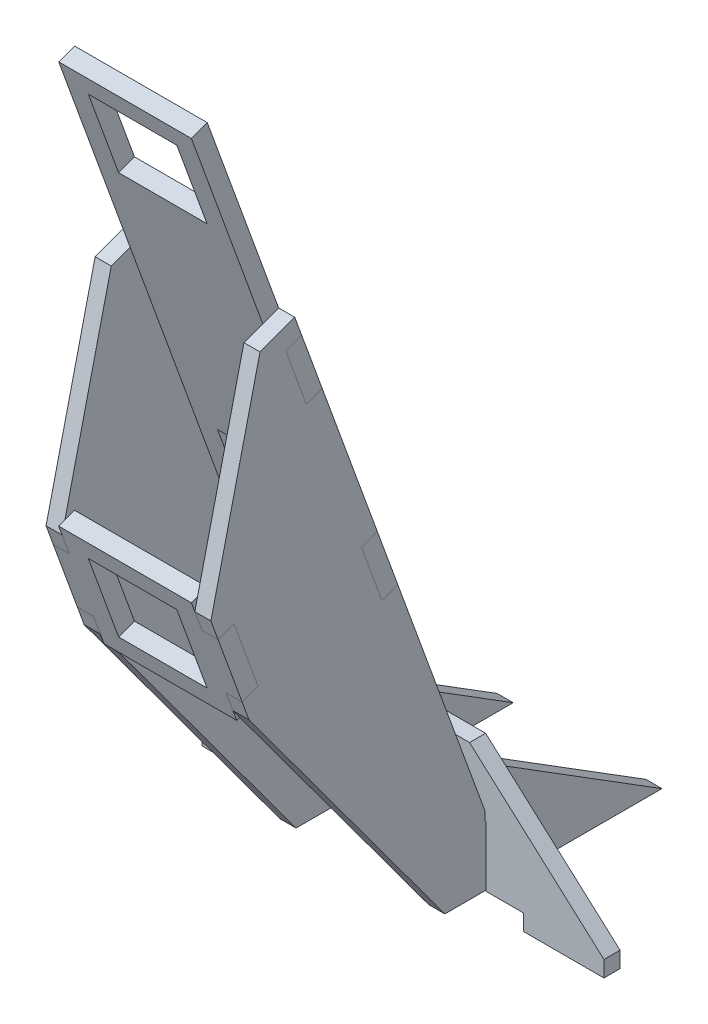
SolidWorks part; units mm, degrees
ref_plane "Front Plane" through (0, 0, 0) normal (0, 0, 1) x (1, 0, 0)
ref_plane "Top Plane" through (0, 0, 0) normal (0, 1, 0) x (1, 0, 0)
ref_plane "Right Plane" through (0, 0, 0) normal (1, 0, 0) x (0, 0, -1)
sketch "Sketch2" plane through (-4.2325, 0, 0) normal (-1, 0, 0) x (0, 0, 1)
  line L0 (-218.5461, -194.3785) -> (8.2017, -276.908) construction
  line L1 (-1207.3778, 14.2537) -> (0.4005, -425.3416) construction
  line L2 (-218.5461, -321.3785) -> (8.2017, -403.908) construction
  line L3 (-1207.3778, 141.2537) -> (0.4005, -298.3416) construction
  line L4 (-208.1635, -198.1575) -> (8.2017, -276.908)
  line L5 (-207.799, -349.5632) -> (0.4005, -425.3416)
  line L6 (-208.0044, -325.2154) -> (8.2017, -403.908)
  line L7 (-208.2509, -222.3987) -> (0.4005, -298.3416)
  spline S0 degree 3 poles (189.4409, -3120.4084) (-13.0982, -2399.0287) (-141.5864, -1647.8741) (-189.7389, -873.9266) (-192.938, -817.645) (-195.5222, -767.4363) (-197.2853, -729.899) (-199.779, -673.587) (-201.7119, -622.7867) (-203.4957, -566.448) (-206.2171, -472.5416) (-207.9041, -370.9386) (-208.259, -276.9662) (-208.2899, -248.7729) (-208.2187, -160.2224) (-207.0238, -66.2188) (-203.9584, 56.001) (-202.3756, 119.8355) (-200.5061, 195.0475) (-179.7563, 1029.0685) (-159.4327, 1846.2624) (-139.564, 2642.678) knots -1.099268 -1.099268 -1.099268 -1.099268 0.127744 0.158994 0.190244 0.221494 0.242608 0.252744 0.315244 0.327161 0.346494 0.471494 0.496149 0.502744 0.518369 0.643369 0.658994 0.721494 0.74946 0.783994 2.107611 2.107611 2.107611 2.107611 only from (-169.1687, -1155.1044) to (-189.3532, 643.3419) construction
  spline S1 degree 3 poles (-169.1687, -1155.1044) (-175.6459, -1080.1785) (-182.7373, -986.4616) (-189.7389, -873.9266) (-192.938, -817.645) (-195.5222, -767.4363) (-197.2853, -729.899) (-199.779, -673.587) (-201.7119, -622.7867) (-203.4957, -566.448) (-206.2171, -472.5416) (-207.9041, -370.9386) (-208.259, -276.9662) (-208.2899, -248.7729) (-208.2187, -160.2224) (-207.0238, -66.2188) (-203.9584, 56.001) (-202.3756, 119.8355) (-200.5061, 195.0475) (-196.3369, 362.6233) (-192.5867, 513.3721) (-189.3532, 643.3419) knots 0.002744 0.002744 0.002744 0.002744 0.127744 0.158994 0.190244 0.221494 0.242608 0.252744 0.315244 0.327161 0.346494 0.471494 0.496149 0.502744 0.518369 0.643369 0.658994 0.721494 0.74946 0.783994 1 1 1 1
sketch "Sketch3" plane through (0, 0, 0) normal (1, 0, 0) x (0, 0, -1)
  line L0 (-6.4471, -266.1331) -> (-11.4594, -267.9574)
  line L1 (-6.4471, -266.1331) -> (48.6866, -417.6117)
  line L2 (-11.4594, -267.9574) -> (43.6743, -419.436)
  line L3 (48.6866, -417.6117) -> (43.6743, -419.436)
  line L5 (208.1635, -198.1575) -> (-8.2017, -276.908) construction
  line L6 (207.799, -349.5632) -> (-0.4005, -425.3416) construction
  line L7 (7.8696, -432.4678) -> (2.8573, -434.2922)
  line L8 (7.8696, -432.4678) -> (-6.4471, -393.1331)
  line L9 (2.8573, -434.2922) -> (-11.4594, -394.9574)
  line L10 (-6.4471, -393.1331) -> (-11.4594, -394.9574)
  line L11 (208.0044, -325.2154) -> (-8.2017, -403.908) construction
  point P9 (46.1804, -418.5238)
  dimension "D1" = 5.334
  dimension "D2" = 9.525
  dimension "D3" = 9.525
  dimension "D4" = 9.525
extrude "Boss-Extrude1" add sketch "Sketch3" against normal blind 13.335 and the other way blind 28.575 contours L2 L3 L1 L0
sketch "Sketch4" plane through (0, -33.2037, 91.2265) normal (0, 0.342, -0.9397) x (-1, 0, 0)
  line L0 (3.7846, -399.5534) -> (-19.0246, -399.5534) construction
  line L1 (3.7846, -399.5534) -> (3.7846, -376.7442) construction
  line L2 (-19.0246, -399.5534) -> (-19.0246, -376.7442) construction
  line L3 (3.7846, -376.7442) -> (-19.0246, -376.7442) construction
  line L4 (3.7846, -280.2124) -> (3.7846, -257.4032) construction
  line L5 (3.7846, -280.2124) -> (-19.0246, -280.2124) construction
  line L6 (3.7846, -257.4032) -> (-19.0246, -257.4032) construction
  line L7 (-19.0246, -280.2124) -> (-19.0246, -257.4032) construction
  line L9 (-28.575, -409.0784) -> (13.335, -409.0784) construction
  line L10 (-21.59, -282.7778) -> (-21.59, -254.8378)
  line L11 (6.35, -254.8378) -> (-21.59, -254.8378)
  line L12 (6.35, -282.7778) -> (6.35, -254.8378)
  line L13 (6.35, -282.7778) -> (-21.59, -282.7778)
  line L14 (6.35, -374.1788) -> (-21.59, -374.1788)
  line L15 (-21.59, -402.1188) -> (-21.59, -374.1788)
  line L16 (6.35, -402.1188) -> (-21.59, -402.1188)
  line L17 (6.35, -402.1188) -> (6.35, -374.1788)
  point P0 (4.2325, -399.5534)
  point P3 (4.2325, -376.7442)
  point P6 (4.2325, -280.2124)
  point P9 (4.2325, -257.4032)
  point P19 (-7.62, -399.5534)
  point P22 (-7.62, -409.0784)
  dimension "D1" = 27.94
  dimension "D2" = 27.94
extrude "Cut-Extrude1" cut sketch "Sketch4" against normal through all
sketch "Sketch5" plane through (0, -515.0244, 0) normal (0, 1, 0) x (1, 0, 0)
  line L0 (223.6182, 76.2) -> (198.2182, 76.2) construction
  line L1 (198.2182, 81.28) -> (223.6182, 81.28) construction
  line L2 (172.8182, 76.2) -> (147.4182, 76.2) construction
  line L3 (147.4182, 81.28) -> (172.8182, 81.28) construction
  line L4 (20.4182, 198.4309) -> (-4.9818, 198.4309)
  line L5 (-4.9818, 198.4309) -> (-4.9818, 204.5203)
  line L6 (-219.8374, 5.08) -> (235.2738, 5.08)
  line L7 (20.4182, 204.5202) -> (20.4182, 198.4309)
  line L8 (20.4182, 198.4309) -> (-4.9818, 198.4309)
  line L9 (-4.9818, 198.4309) -> (-4.9818, 204.5203)
  line L10 (-219.8374, 5.08) -> (235.2738, 5.08)
  line L11 (20.4182, 204.5202) -> (20.4182, 198.4309)
  line L12 (122.0182, 76.2) -> (96.6182, 76.2) construction
  line L13 (96.6182, 81.28) -> (122.0182, 81.28) construction
  line L14 (45.8182, 81.28) -> (71.2182, 81.28) construction
  line L15 (71.2182, 76.2) -> (45.8182, 76.2) construction
  line L16 (20.4182, 76.2) -> (-4.9818, 76.2) construction
  line L17 (-4.9818, 81.28) -> (20.4182, 81.28) construction
  line L18 (-30.3818, 76.2) -> (-55.7818, 76.2) construction
  line L19 (-55.7818, 81.28) -> (-30.3818, 81.28) construction
  line L20 (-81.1818, 76.2) -> (-106.5818, 76.2) construction
  line L21 (-106.5818, 81.28) -> (-81.1818, 81.28) construction
  line L22 (-131.9818, 76.2) -> (-157.3818, 76.2) construction
  line L23 (-157.3818, 81.28) -> (-131.9818, 81.28) construction
  line L24 (-182.7818, 76.2) -> (-208.1818, 76.2) construction
  line L25 (-208.1818, 81.28) -> (-182.7818, 81.28) construction
  line L26 (-208.1818, 81.28) -> (-182.7818, 81.28)
  line L27 (-182.7818, 76.2) -> (-208.1818, 76.2)
  line L28 (-157.3818, 81.28) -> (-131.9818, 81.28)
  line L29 (-131.9818, 76.2) -> (-157.3818, 76.2)
  line L30 (-106.5818, 81.28) -> (-81.1818, 81.28)
  line L31 (-81.1818, 76.2) -> (-106.5818, 76.2)
  line L32 (-55.7818, 81.28) -> (-30.3818, 81.28)
  line L33 (-30.3818, 76.2) -> (-55.7818, 76.2)
  line L34 (-4.9818, 81.28) -> (20.4182, 81.28)
  line L35 (20.4182, 76.2) -> (-4.9818, 76.2)
  line L36 (45.8182, 81.28) -> (71.2182, 81.28)
  line L37 (71.2182, 76.2) -> (45.8182, 76.2)
  line L38 (96.6182, 81.28) -> (122.0182, 81.28)
  line L39 (122.0182, 76.2) -> (96.6182, 76.2)
  line L40 (147.4182, 81.28) -> (172.8182, 81.28)
  line L41 (172.8182, 76.2) -> (147.4182, 76.2)
  line L42 (198.2182, 81.28) -> (223.6182, 81.28)
  line L43 (223.6182, 76.2) -> (198.2182, 76.2)
  spline S2 degree 3 poles (1842.4663, -3260.0665) (948.577, -533.6156) (383.6873, 261.2248) (-42.8345, 200.7019) (-49.9403, 199.4383) (-64.0669, 196.4116) (-71.0878, 194.6489) (-81.5541, 191.6239) (-85.0321, 190.552) (-90.2326, 188.8477) (-91.9634, 188.2636) (-95.4194, 187.0627) (-97.1424, 186.4468) (-105.7114, 183.2977) (-112.4394, 180.5492) (-132.2531, 171.6351) (-144.9698, 164.804) (-163.3071, 153.2264) (-169.2964, 149.1452) (-178.0924, 142.6841) (-180.993, 140.4738) (-185.2959, 137.0716) (-186.7221, 135.9231) (-188.4878, 134.475) (-188.8401, 134.1847) (-189.5433, 133.6027) (-189.8953, 133.312) (-190.9356, 132.426) (-191.6104, 131.8185) (-194.8949, 128.7004) (-197.2373, 125.9495) (-199.8047, 122.1867) (-200.3, 121.4179) (-201.2541, 119.8473) (-201.7134, 119.0436) (-203.0281, 116.5915) (-203.806, 114.93) (-205.1764, 111.5567) (-205.768, 109.8447) (-206.7675, 106.3707) (-207.1764, 104.6091) (-207.5683, 102.3747) (-207.6407, 101.9262) (-207.7733, 101.0259) (-207.8317, 100.5736) (-208.0056, 99.2163) (-208.1214, 98.3115) (-208.4688, 95.5968) (-208.7001, 93.787) (-356.7457, -1065.9382) (-390.3223, -2238.1969) (-2268.9649, -3178.7947) knots -3.541724 -3.541724 -3.541724 -3.541724 0.125 0.125 0.1875 0.1875 0.25 0.25 0.28125 0.28125 0.296875 0.296875 0.3125 0.3125 0.375 0.375 0.5 0.5 0.5625 0.5625 0.59375 0.59375 0.609375 0.609375 0.613281 0.613281 0.617188 0.617188 0.625 0.625 0.65625 0.65625 0.664063 0.664063 0.671875 0.671875 0.6875 0.6875 0.703125 0.703125 0.71875 0.71875 0.722656 0.722656 0.726563 0.726563 0.734375 0.734375 0.75 0.75 10.746502 10.746502 10.746502 10.746502 only from (-4.9818, 204.5203) to (-219.8374, 5.08)
  spline S3 degree 3 poles (2354.6207, -3093.6099) (407.0316, -2276.1632) (374.4311, -1083.5388) (224.132, 93.8227) (223.7849, 96.5384) (223.4372, 99.2541) (223.2632, 100.6119) (223.2044, 101.0644) (223.0708, 101.9667) (222.9978, 102.4169) (222.6018, 104.6625) (222.1869, 106.4428) (221.4197, 109.0896) (221.1394, 109.9678) (220.5289, 111.7161) (220.1999, 112.5817) (218.4502, 116.8405) (216.7095, 120.0562) (214.1102, 123.8382) (213.5687, 124.5824) (212.4417, 126.0462) (211.8552, 126.7671) (210.0517, 128.8641) (208.7846, 130.1839) (206.7909, 132.0516) (206.1106, 132.6552) (205.0667, 133.5322) (204.7161, 133.8213) (204.0152, 134.4001) (202.2598, 135.8431) (200.4883, 137.2667) (196.2056, 140.646) (193.3094, 142.8493) (187.4346, 147.1565) (184.4517, 149.2632) (178.4338, 153.3562) (175.3969, 155.344) (166.2039, 161.1335) (159.965, 164.7612) (147.2712, 171.561) (140.8164, 174.7336) (121.1292, 183.5717) (107.5758, 188.5606) (91.8269, 193.1168) (90.0694, 193.6084) (86.553, 194.5586) (84.7927, 195.0175) (79.5049, 196.3465) (75.9708, 197.1686) (65.3426, 199.4454) (58.2221, 200.7102) (-388.5399, 264.0224) (-958.4281, -616.7535) (-1775.0229, -3283.3786) knots -9.89492 -9.89492 -9.89492 -9.89492 0.25 0.25 0.265625 0.273438 0.273438 0.277344 0.277344 0.28125 0.28125 0.296875 0.296875 0.304688 0.304688 0.3125 0.3125 0.34375 0.34375 0.351563 0.351563 0.359375 0.359375 0.375 0.375 0.382813 0.382813 0.386719 0.386719 0.390625 0.40625 0.40625 0.4375 0.4375 0.46875 0.46875 0.5 0.5 0.5625 0.5625 0.625 0.625 0.75 0.75 0.765625 0.765625 0.78125 0.78125 0.8125 0.8125 0.875 0.875 4.714976 4.714976 4.714976 4.714976 only from (235.2738, 5.08) to (20.4182, 204.5202)
  spline S4 degree 3 poles (-4.9818, 204.5203) (-15.3035, 204.0961) (-25.5375, 203.1563) (-42.8345, 200.7019) (-49.9403, 199.4383) (-64.0669, 196.4116) (-71.0878, 194.6489) (-81.5541, 191.6239) (-85.0321, 190.552) (-90.2326, 188.8477) (-91.9634, 188.2636) (-95.4194, 187.0627) (-97.1424, 186.4468) (-105.7114, 183.2977) (-112.4394, 180.5492) (-132.2531, 171.6351) (-144.9698, 164.804) (-163.3071, 153.2264) (-169.2964, 149.1452) (-178.0924, 142.6841) (-180.993, 140.4738) (-185.2959, 137.0716) (-186.7221, 135.9231) (-188.4878, 134.475) (-188.8401, 134.1847) (-189.5433, 133.6027) (-189.8953, 133.312) (-190.9356, 132.426) (-191.6104, 131.8185) (-194.8949, 128.7004) (-197.2373, 125.9495) (-199.8047, 122.1867) (-200.3, 121.4179) (-201.2541, 119.8473) (-201.7134, 119.0436) (-203.0281, 116.5915) (-203.806, 114.93) (-205.1764, 111.5567) (-205.768, 109.8447) (-206.7675, 106.3707) (-207.1764, 104.6091) (-207.5683, 102.3747) (-207.6407, 101.9262) (-207.7733, 101.0259) (-207.8317, 100.5736) (-208.0056, 99.2163) (-208.1214, 98.3115) (-208.4688, 95.5968) (-208.7001, 93.787) (-212.6278, 63.0191) (-216.253, 34.0521) (-219.8374, 5.08) knots 0.036266 0.036266 0.036266 0.036266 0.125 0.125 0.1875 0.1875 0.25 0.25 0.28125 0.28125 0.296875 0.296875 0.3125 0.3125 0.375 0.375 0.5 0.5 0.5625 0.5625 0.59375 0.59375 0.609375 0.609375 0.613281 0.613281 0.617188 0.617188 0.625 0.625 0.65625 0.65625 0.664063 0.664063 0.671875 0.671875 0.6875 0.6875 0.703125 0.703125 0.71875 0.71875 0.722656 0.722656 0.726563 0.726563 0.734375 0.734375 0.75 0.75 1 1 1 1
  spline S5 degree 3 poles (235.2738, 5.08) (231.688, 34.0638) (228.0612, 63.0431) (224.132, 93.8227) (223.7849, 96.5384) (223.4372, 99.2541) (223.2632, 100.6119) (223.2044, 101.0644) (223.0708, 101.9667) (222.9978, 102.4169) (222.6018, 104.6625) (222.1869, 106.4428) (221.4197, 109.0896) (221.1394, 109.9678) (220.5289, 111.7161) (220.1999, 112.5817) (218.4502, 116.8405) (216.7095, 120.0562) (214.1102, 123.8382) (213.5687, 124.5824) (212.4417, 126.0462) (211.8552, 126.7671) (210.0517, 128.8641) (208.7846, 130.1839) (206.7909, 132.0516) (206.1106, 132.6552) (205.0667, 133.5322) (204.7161, 133.8213) (204.0152, 134.4001) (202.2598, 135.8431) (200.4883, 137.2667) (196.2056, 140.646) (193.3094, 142.8493) (187.4346, 147.1565) (184.4517, 149.2632) (178.4338, 153.3562) (175.3969, 155.344) (166.2039, 161.1335) (159.965, 164.7612) (147.2712, 171.561) (140.8164, 174.7336) (121.1292, 183.5717) (107.5758, 188.5606) (91.8269, 193.1168) (90.0694, 193.6084) (86.553, 194.5586) (84.7927, 195.0175) (79.5049, 196.3465) (75.9708, 197.1686) (65.3426, 199.4454) (58.2221, 200.7102) (40.9206, 203.162) (30.7048, 204.0975) (20.4182, 204.5202) knots 0 0 0 0 0.25 0.25 0.265625 0.273438 0.273438 0.277344 0.277344 0.28125 0.28125 0.296875 0.296875 0.304688 0.304688 0.3125 0.3125 0.34375 0.34375 0.351563 0.351563 0.359375 0.359375 0.375 0.375 0.382813 0.382813 0.386719 0.386719 0.390625 0.40625 0.40625 0.4375 0.4375 0.46875 0.46875 0.5 0.5 0.5625 0.5625 0.625 0.625 0.75 0.75 0.765625 0.765625 0.78125 0.78125 0.8125 0.8125 0.875 0.875 0.963629 0.963629 0.963629 0.963629
  dimension "D1" = 0
ref_plane "Plane1" through (0, 0, -76.2) normal (0, 0, 1) x (1, 0, 0)
sketch "Sketch6" plane through (0, 0, -76.2) normal (0, 0, 1) x (1, 0, 0)
  line L0 (71.2182, -515.0244) -> (45.8182, -515.0244)
  line L1 (71.2182, -515.0244) -> (71.2182, -520.1044)
  line L2 (45.8182, -515.0244) -> (45.8182, -520.1044)
  line L3 (71.2182, -520.1044) -> (45.8182, -520.1044)
  line L4 (20.4182, -515.0244) -> (-4.9818, -515.0244)
  line L5 (20.4182, -515.0244) -> (20.4182, -520.1044)
  line L6 (-4.9818, -515.0244) -> (-4.9818, -520.1044)
  line L7 (20.4182, -520.1044) -> (-4.9818, -520.1044)
  line L8 (-30.3818, -515.0244) -> (-55.7818, -515.0244)
  line L9 (-30.3818, -515.0244) -> (-30.3818, -520.1044)
  line L10 (-55.7818, -515.0244) -> (-55.7818, -520.1044)
  line L11 (-30.3818, -520.1044) -> (-55.7818, -520.1044)
  line L12 (45.8182, -515.0244) -> (20.4182, -515.0244)
  line L13 (-4.9818, -515.0244) -> (-30.3818, -515.0244)
  line L14 (-55.7818, -515.0244) -> (-13.335, -476.9244)
  line L15 (-13.335, -476.9244) -> (28.7714, -476.9244)
  line L16 (28.7714, -476.9244) -> (71.2182, -515.0244)
  line L17 (-13.335, -267.9574) -> (-13.335, -419.436) construction
  dimension "D1" = 5.08
  dimension "D2" = 38.1
extrude "Boss-Extrude2" add sketch "Sketch6" against normal blind 5.08 separate body contours L16 L15 L14 L8 L13 L4 L12 L0 | L3 L1 L0 L2 | L7 L5 L4 L6 | L11 L9 L8 L10
sketch "Sketch7" plane through (0, 0, -76.2) normal (0, 0, 1) x (1, 0, 0)
  line L0 (28.575, -515.0244) -> (33.909, -515.0244)
  line L1 (28.575, -515.0244) -> (28.575, -495.9744)
  line L2 (33.909, -515.0244) -> (33.909, -495.9744)
  line L3 (28.575, -495.9744) -> (33.909, -495.9744)
  line L4 (45.8182, -515.0244) -> (20.4182, -515.0244) construction
  line L5 (-13.335, -515.0244) -> (-18.669, -515.0244)
  line L6 (-13.335, -515.0244) -> (-13.335, -495.9744)
  line L7 (-18.669, -515.0244) -> (-18.669, -495.9744)
  line L8 (-13.335, -495.9744) -> (-18.669, -495.9744)
  line L9 (-4.9818, -515.0244) -> (-30.3818, -515.0244) construction
  line L10 (28.575, -267.9574) -> (28.575, -419.436) construction
  line L11 (-13.335, -267.9574) -> (-13.335, -419.436) construction
  dimension "D1" = 5.334
  dimension "D2" = 19.05
extrude "Cut-Extrude2" cut sketch "Sketch7" against normal through all
sketch "Sketch8" plane through (0, -49.8842, 137.0558) normal (0, -0.342, 0.9397) x (1, 0, 0)
  line L0 (-13.335, -377.0363) -> (-13.335, -399.2613)
  line L1 (-13.335, -377.0363) -> (-18.415, -377.0363)
  line L2 (-13.335, -399.2613) -> (-18.415, -399.2613)
  line L3 (-18.415, -377.0363) -> (-18.415, -399.2613)
  line L4 (-13.335, -367.2192) -> (-13.335, -409.0784) construction
  line L5 (28.575, -377.0363) -> (28.575, -399.2613)
  line L6 (28.575, -377.0363) -> (33.655, -377.0363)
  line L7 (28.575, -399.2613) -> (33.655, -399.2613)
  line L8 (33.655, -377.0363) -> (33.655, -399.2613)
  line L9 (28.575, -367.2192) -> (28.575, -409.0784) construction
  point P12 (28.575, -388.1488)
  point P13 (-13.335, -388.1488)
  dimension "D1" = 5.08
  dimension "D2" = 22.225
extrude "Boss-Extrude3" add sketch "Sketch8" against normal up to surface (5.334 mm away) up to face at (7.62, -412.8005, -0.7112)
sketch "Sketch10" plane through (0, -35.0281, 96.2388) normal (0, -0.342, 0.9397) x (1, 0, 0)
  line L0 (-13.335, -409.0784) -> (-13.335, -390.0284)
  line L1 (-13.335, -409.0784) -> (-18.415, -409.0784)
  line L2 (-13.335, -390.0284) -> (-18.415, -390.0284)
  line L3 (-18.415, -409.0784) -> (-18.415, -390.0284)
  line L4 (-13.335, -247.8782) -> (-13.335, -409.0784) construction
  line L5 (28.575, -409.0784) -> (28.575, -390.0284)
  line L6 (28.575, -409.0784) -> (33.655, -409.0784)
  line L7 (28.575, -390.0284) -> (33.655, -390.0284)
  line L8 (33.655, -409.0784) -> (33.655, -390.0284)
  line L9 (28.575, -247.8782) -> (28.575, -409.0784) construction
  line L10 (-13.335, -320.1784) -> (-13.335, -339.2284)
  line L11 (-13.335, -320.1784) -> (-18.415, -320.1784)
  line L12 (-13.335, -339.2284) -> (-18.415, -339.2284)
  line L13 (-18.415, -320.1784) -> (-18.415, -339.2284)
  line L14 (28.575, -320.1784) -> (28.575, -339.2284)
  line L15 (28.575, -320.1784) -> (33.655, -320.1784)
  line L16 (28.575, -339.2284) -> (33.655, -339.2284)
  line L17 (33.655, -320.1784) -> (33.655, -339.2284)
  dimension "D1" = 5.08
  dimension "D2" = 19.05
  dimension "D3" = 88.9
extrude "Boss-Extrude4" add sketch "Sketch10" against normal up to surface (5.334 mm away) up to face at (7.62, -285.8005, -0.7112)
sketch "Sketch11" plane through (-13.335, 0, 0) normal (-1, 0, 0) x (0, 0, 1)
  line L0 (-16.1092, -328.1059) -> (-5.1298, -332.1021)
  line L1 (10.3735, -397.9409) -> (-1.6714, -431.0342)
  line L3 (-16.1092, -328.1059) -> (-76.2, -493.2041)
  line L4 (-42.1711, -399.7105) -> (-24.7965, -351.9741) construction
  line L5 (-76.2, -493.2041) -> (-76.2, -495.9744)
  line L8 (-63.5, -515.0244) -> (-132.08, -515.0244)
  line L9 (-132.08, -515.0244) -> (-81.28, -483.2744)
  line L10 (10.3735, -397.9409) -> (-5.1298, -332.1021)
  line L12 (-208.0044, -325.2154) -> (8.2017, -403.908) construction
  line L13 (-81.28, -483.2744) -> (-81.28, -495.9744)
  line L14 (-81.28, -495.9744) -> (-76.2, -495.9744)
  line L15 (-81.28, -495.9744) -> (-76.2, -495.9744) construction
  line L16 (-18.281, -334.073) -> (-13.2687, -335.8973) construction
  line L17 (-13.2687, -335.8973) -> (-19.7842, -353.7985) construction
  line L18 (-18.281, -334.073) -> (-24.7965, -351.9741) construction
  line L19 (-24.7965, -351.9741) -> (-19.7842, -353.7985) construction
  line L20 (-19.7842, -353.7985) -> (-13.2687, -335.8973) construction
  line L21 (-13.2687, -335.8973) -> (-18.281, -334.073) construction
  line L22 (3.0895, -402.3581) -> (-4.5119, -423.2428) construction
  line L23 (-4.5119, -423.2428) -> (0.5004, -425.0671) construction
  line L24 (0.5004, -425.0671) -> (8.1018, -404.1825) construction
  line L25 (8.1018, -404.1825) -> (3.0895, -402.3581) construction
  line L26 (-42.1711, -399.7105) -> (-48.6866, -417.6117) construction
  line L27 (-48.6866, -417.6117) -> (-43.6743, -419.436) construction
  line L28 (-43.6743, -419.436) -> (-37.1588, -401.5349) construction
  line L29 (-37.1588, -401.5349) -> (-42.1711, -399.7105) construction
  line L30 (-18.281, -334.073) -> (-24.7965, -351.9741)
  line L31 (-24.7965, -351.9741) -> (-19.7842, -353.7985)
  line L32 (-19.7842, -353.7985) -> (-13.2687, -335.8973)
  line L33 (-13.2687, -335.8973) -> (-18.281, -334.073)
  line L34 (3.0895, -402.3581) -> (-4.5119, -423.2428)
  line L35 (-4.5119, -423.2428) -> (0.5004, -425.0671)
  line L36 (0.5004, -425.0671) -> (8.1018, -404.1825)
  line L37 (8.1018, -404.1825) -> (3.0895, -402.3581)
  line L38 (-42.1711, -399.7105) -> (-48.6866, -417.6117)
  line L39 (-48.6866, -417.6117) -> (-43.6743, -419.436)
  line L40 (-43.6743, -419.436) -> (-37.1588, -401.5349)
  line L41 (-37.1588, -401.5349) -> (-42.1711, -399.7105)
  line L42 (-1.6714, -431.0342) -> (-63.5, -515.0244)
  line L43 (-76.2, -515.0244) -> (-76.2, -476.9244) construction
  line L44 (-81.28, -515.0244) -> (-76.2, -515.0244) construction
  point P44 (-78.74, -515.0244)
  line M11 (-18.281, -334.073) -> (-13.2687, -335.8973)
  line M12 (-13.2687, -335.8973) -> (11.4594, -267.9574)
  line M14 (6.4471, -266.1331) -> (-18.281, -334.073)
  dimension "D3" = 6.35
  dimension "D4" = 6.35
  dimension "D5" = 6.35
  dimension "D6" = 12.7
  dimension "D7" = 6.35
  dimension "D8" = 50.8
  dimension "D9" = 12.7
extrude "Boss-Extrude5" add sketch "Sketch11" along normal blind 5.08 separate body contours L42 L1 L35 L34 L37 L10 L0 L32 L31 L3 L41 L40 L39 L5 L14 L13 L9 L8 M12 | L0 M14 M11 M12
ref_plane "Plane2" through (7.62, 0, 0) normal (-1, 0, 0) x (0, 0, 1)
mirror "Mirror1" about plane through (7.62, 0, 0) normal (-1, 0, 0) of bodies 111
delete or keep bodies "Body-Delete/Keep 1" [suppressed] type keep bodies bodies 108
delete or keep bodies "Body-Delete/Keep 2" [suppressed] type keep bodies bodies 110
delete or keep bodies "Body-Delete/Keep 3" [suppressed] type keep bodies bodies 111
delete or keep bodies "Body-Delete/Keep 4" [suppressed] type keep bodies bodies 109
